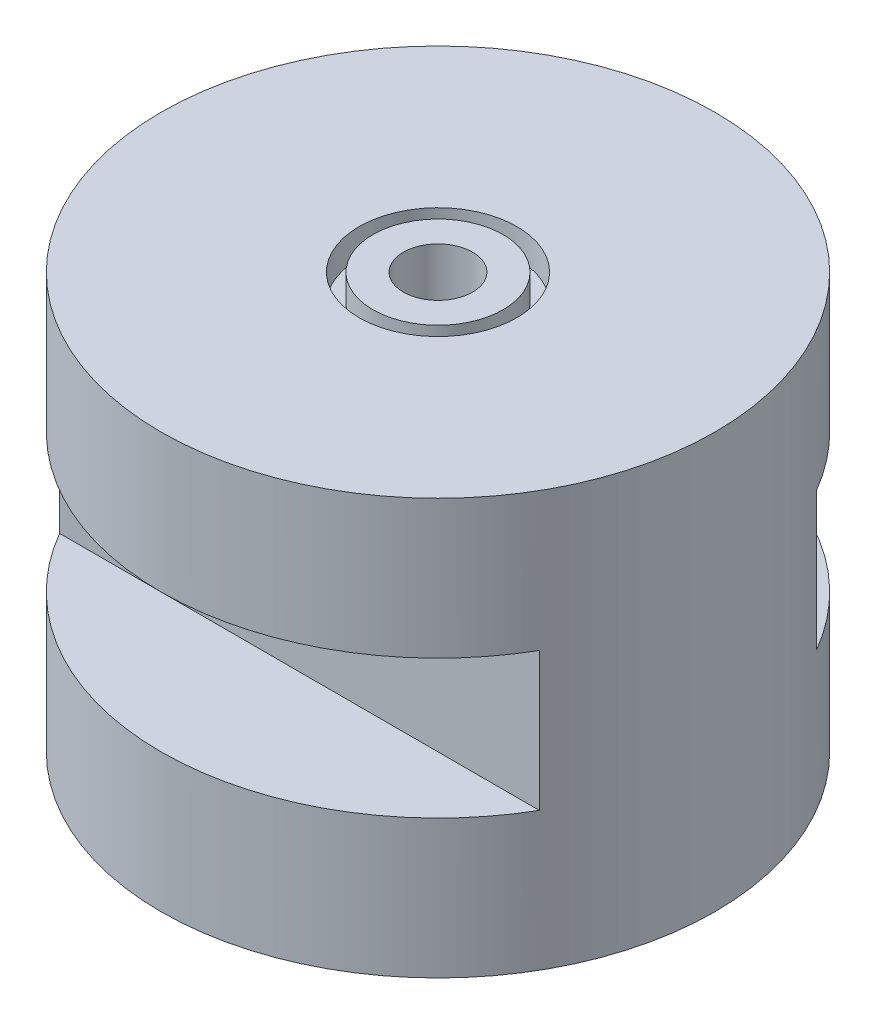
SolidWorks part; units mm, degrees
ref_plane "Plan de face" through (0, 0, 0) normal (0, 0, 1) x (1, 0, 0)
ref_plane "Plan de dessus" through (0, 0, 0) normal (0, 1, 0) x (1, 0, 0)
ref_plane "Plan de droite" through (0, 0, 0) normal (1, 0, 0) x (0, 0, -1)
sketch "Esquisse1" plane through (0, 0, 0) normal (0, 1, 0) x (1, 0, 0)
  circle A0 centre (0, 0) radius 10
  dimension "D1" = 20
extrude "Boss.-Extru.1" add sketch "Esquisse1" along normal blind 15
sketch "Esquisse2" plane through (0, 15, 0) normal (0, 1, 0) x (1, 0, 0)
  circle A0 centre (0, 0) radius 2.85
  circle A1 centre (0, 0) radius 2.35
  dimension "D1" = 5.7
  dimension "D2" = 0.5
extrude "Enlèv. mat.-Extru.1" cut sketch "Esquisse2" against normal blind 1
sketch "Esquisse3" plane through (0, 15, 0) normal (0, 1, 0) x (1, 0, 0)
  circle A0 centre (0, 0) radius 1.25
  dimension "D1" = 2.5
extrude "Enlèv. mat.-Extru.2" cut sketch "Esquisse3" against normal through all
sketch "Esquisse4" plane through (0, 0, 0) normal (1, 0, 0) x (0, 0, -1)
  line L4 (10, 0) -> (10, 15) construction
  line L5 (-10, 15) -> (-10, 0) construction
  line L6 (-10, 5) -> (-5, 5)
  line L7 (-10, 5) -> (-10, 10)
  line L8 (-10, 10) -> (-5, 10)
  line L9 (5, 10) -> (10, 10)
  line L10 (5, 10) -> (5, 5)
  line L11 (5, 5) -> (10, 5)
  line L12 (10, 10) -> (10, 5)
  line L13 (-5, 5) -> (-5, 10)
  line L15 (-10, 0) -> (10, 0) construction
  dimension "D2" = 5
  dimension "D1" = 10
  dimension "D3" = 5
  dimension "D4" = 5
  dimension "D5" = 5
  dimension "D7" = 5
  dimension "D8" = 5
extrude "Enlèv. mat.-Extru.3" cut sketch "Esquisse4" against normal through all both and the other way through all
